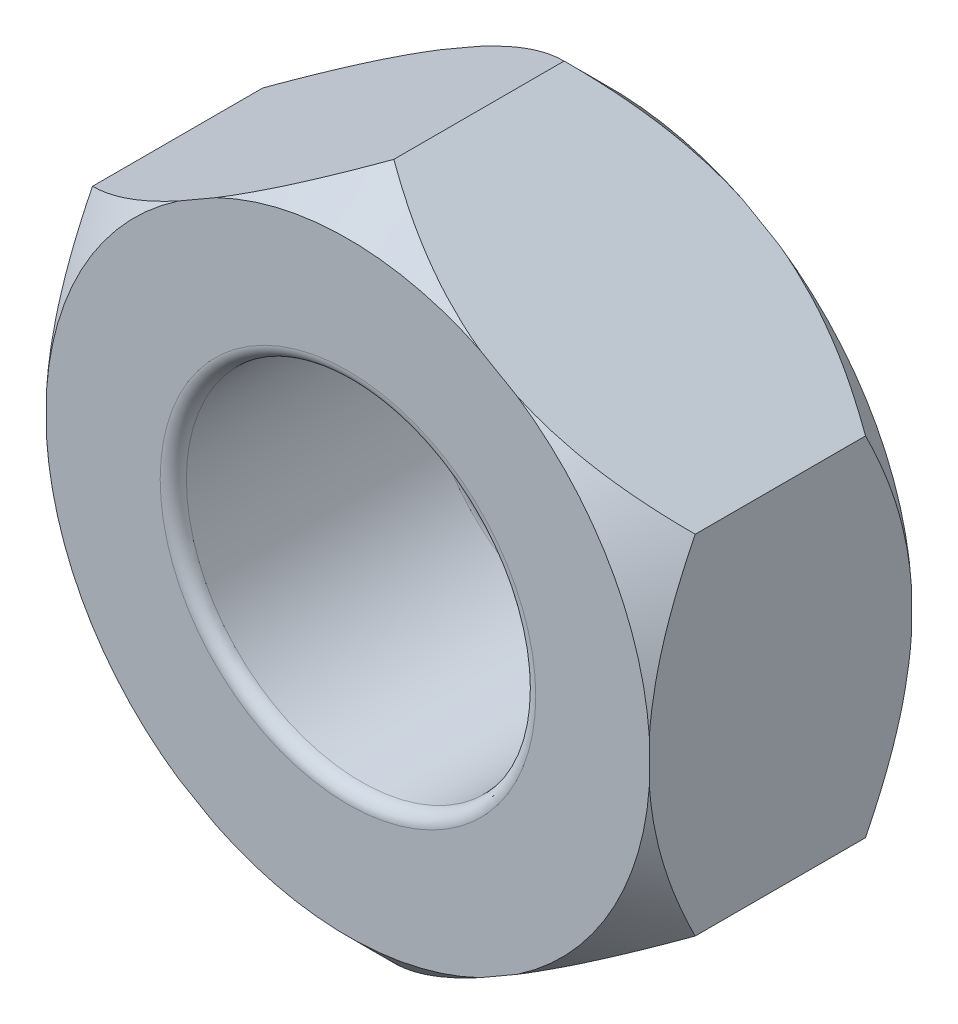
SolidWorks part; units mm, degrees
ref_plane "前视基准面" through (0, 0, 0) normal (0, 0, 1) x (1, 0, 0)
ref_plane "上视基准面" through (0, 0, 0) normal (0, 1, 0) x (1, 0, 0)
ref_plane "右视基准面" through (0, 0, 0) normal (1, 0, 0) x (0, 0, -1)
sketch "草图1" plane through (0, 0, 0) normal (0, 0, 1) x (1, 0, 0)
  line L1 (0, 7.9674) -> (-6.9, 3.9837)
  line L2 (-6.9, 3.9837) -> (-6.9, -3.9837)
  line L3 (-6.9, -3.9837) -> (0, -7.9674)
  line L4 (0, -7.9674) -> (6.9, -3.9837)
  line L5 (6.9, -3.9837) -> (6.9, 3.9837)
  line L6 (6.9, 3.9837) -> (0, 7.9674)
  circle A0 centre (0, 0) radius 6.9 construction
  dimension "D1" = 13.8
extrude "凸台-拉伸1" add sketch "草图1" against normal blind 6
sketch "草图2" plane through (0, 0, 0) normal (0, 0, 1) x (1, 0, 0)
  circle A0 centre (0, 0) radius 4
extrude "切除-拉伸1" cut sketch "草图2" against normal blind 6
sketch "草图3" plane through (0, 0, 0) normal (1, 0, 0) x (0, 0, -1)
  line L0 (0, 0) -> (8.9814, 0) construction
  line L1 (0, -7.9674) -> (1.05, -7.9674)
  line L2 (6, -7.9674) -> (0, -7.9674) construction
  line L3 (1.05, -7.9674) -> (0, -6.9174)
  line L4 (0, -7.9674) -> (0, -3.9837) construction
  line L5 (0, -6.9174) -> (0, -7.9674)
  line L6 (6, -7.9674) -> (4.95, -7.9674)
  line L7 (4.95, -7.9674) -> (6, -6.9174)
  line L8 (6, -7.9674) -> (6, -3.9837) construction
  line L9 (6, -6.9174) -> (6, -7.9674)
revolve "切除-旋转2" cut sketch "草图3" angle 360 about L0
fillet "圆角3" radius 0.3 2 edges at (4, 0, -6) (4, 0, 0)
